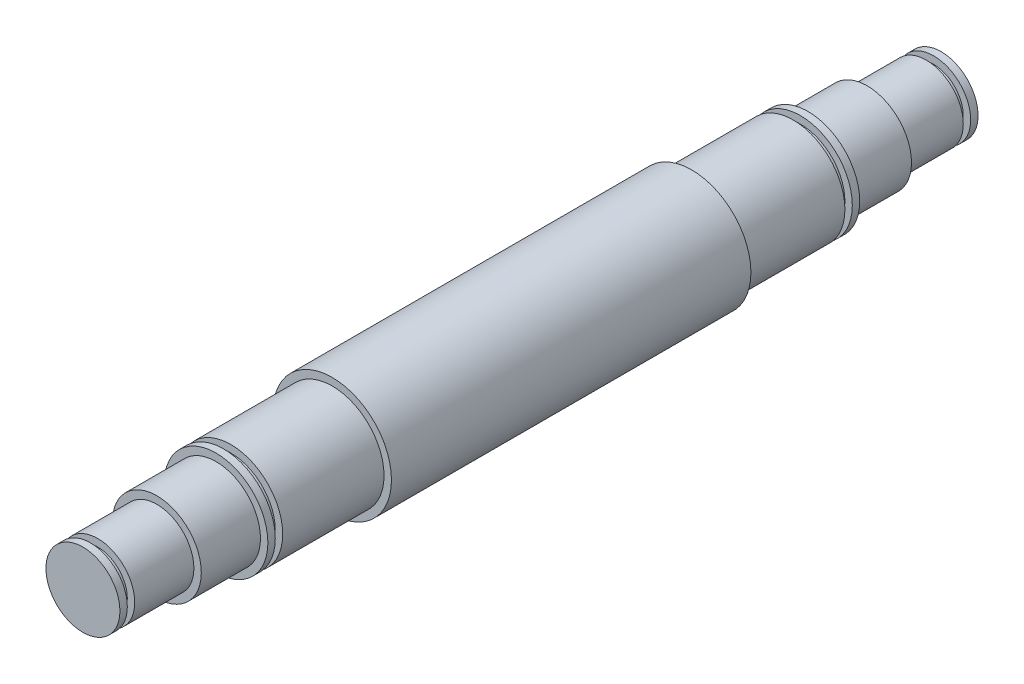
SolidWorks part; units mm, degrees
ref_plane "Front Plane" through (0, 0, 0) normal (0, 0, 1) x (1, 0, 0)
ref_plane "Top Plane" through (0, 0, 0) normal (0, 1, 0) x (1, 0, 0)
ref_plane "Right Plane" through (0, 0, 0) normal (1, 0, 0) x (0, 0, -1)
sketch "Sketch2" plane through (0, 0, 0) normal (0, 0, 1) x (1, 0, 0)
  circle A0 centre (0, 0) radius 15.875
  dimension "D1" = 31.75
extrude "Boss-Extrude1" add sketch "Sketch2" along normal blind 25.4
sketch "Sketch4" plane through (0, 0, 25.4) normal (0, 0, 1) x (1, 0, 0)
  circle A0 centre (0, 0) radius 19.05
  dimension "D1" = 38.1
extrude "Boss-Extrude2" add sketch "Sketch4" along normal blind 25.4
sketch "Sketch5" plane through (0, 0, 50.8) normal (0, 0, 1) x (1, 0, 0)
  circle A0 centre (0, 0) radius 22.225
  dimension "D1" = 44.45
extrude "Boss-Extrude3" add sketch "Sketch5" along normal blind 3.175
sketch "Sketch6" plane through (0, 0, 53.975) normal (0, 0, 1) x (1, 0, 0)
  circle A0 centre (0, 0) radius 19.05
  circle A2 centre (0, 0) radius 22.225 construction
  dimension "D1" = 3.175
extrude "Boss-Extrude4" add sketch "Sketch6" along normal blind 3.175
sketch "Sketch7" plane through (0, 0, 57.15) normal (0, 0, 1) x (1, 0, 0)
  circle A0 centre (0, 0) radius 22.225
  circle A1 centre (0, 0) radius 19.05 construction
  dimension "D1" = 3.175
extrude "Boss-Extrude5" add sketch "Sketch7" along normal blind 43.5102
sketch "Sketch8" plane through (0, 0, 100.6602) normal (0, 0, 1) x (1, 0, 0)
  circle A0 centre (0, 0) radius 25.4
  dimension "D1" = 50.8
extrude "Boss-Extrude6" add sketch "Sketch8" along normal blind 77.1398
ref_plane "Plane1" through (0, -22.225, 0) normal (0, -1, 0) x (-1, 0, 0)
sketch "Sketch9" plane through (0, -22.225, 0) normal (0, -1, 0) x (-1, 0, 0)
  line L0 (-22.225, -57.15) -> (-22.225, -100.6602) construction
  line L1 (0, -69.3801) -> (0, -88.4301) construction
  line L2 (3.175, -69.3801) -> (3.175, -88.4301)
  line L3 (-3.175, -69.3801) -> (-3.175, -88.4301)
  line L4 (-22.225, -57.15) -> (22.225, -57.15) construction
  arc A0 (3.175, -69.3801) -> (-3.175, -69.3801) centre (0, -69.3801) ccw
  arc A1 (-3.175, -88.4301) -> (3.175, -88.4301) centre (0, -88.4301) ccw
  point P6 (0, -78.9051)
  point P11 (0, -57.15)
  point P16 (0, -66.2051)
  point P17 (0, -91.6051)
  point P19 (-22.225, -78.9051)
  dimension "D2" = 3.175
  dimension "D1" = 25.4
extrude "Cut-Extrude1" cut sketch "Sketch9" against normal blind 3.175
mirror "Mirror1" about plane through (0, 0, 177.8) normal (0, 0, 1) of bodies 107
sketch "Sketch10" plane through (0, 0, 0) normal (0, 0, -1) x (-1, 0, 0)
  circle A0 centre (0, 0) radius 12.7
  circle A1 centre (0, 0) radius 15.875 construction
  dimension "D1" = 3.175
extrude "Boss-Extrude7" add sketch "Sketch10" along normal blind 3.175
sketch "Sketch11" plane through (0, 0, -3.175) normal (0, 0, -1) x (-1, 0, 0)
  circle A0 centre (0, 0) radius 15.875
  circle A1 centre (0, 0) radius 12.7 construction
  dimension "D1" = 3.175
extrude "Boss-Extrude8" add sketch "Sketch11" along normal blind 3.175
sketch "Sketch12" plane through (0, 0, 355.6) normal (0, 0, 1) x (1, 0, 0)
  circle A0 centre (0, 0) radius 12.7
  circle A1 centre (0, 0) radius 15.875 construction
  dimension "D1" = 3.175
extrude "Boss-Extrude9" add sketch "Sketch12" along normal blind 3.175
sketch "Sketch13" plane through (0, 0, 358.775) normal (0, 0, 1) x (1, 0, 0)
  circle A0 centre (0, 0) radius 15.875
  circle A1 centre (0, 0) radius 12.7 construction
  dimension "D1" = 3.175
extrude "Boss-Extrude10" add sketch "Sketch13" along normal blind 3.175
